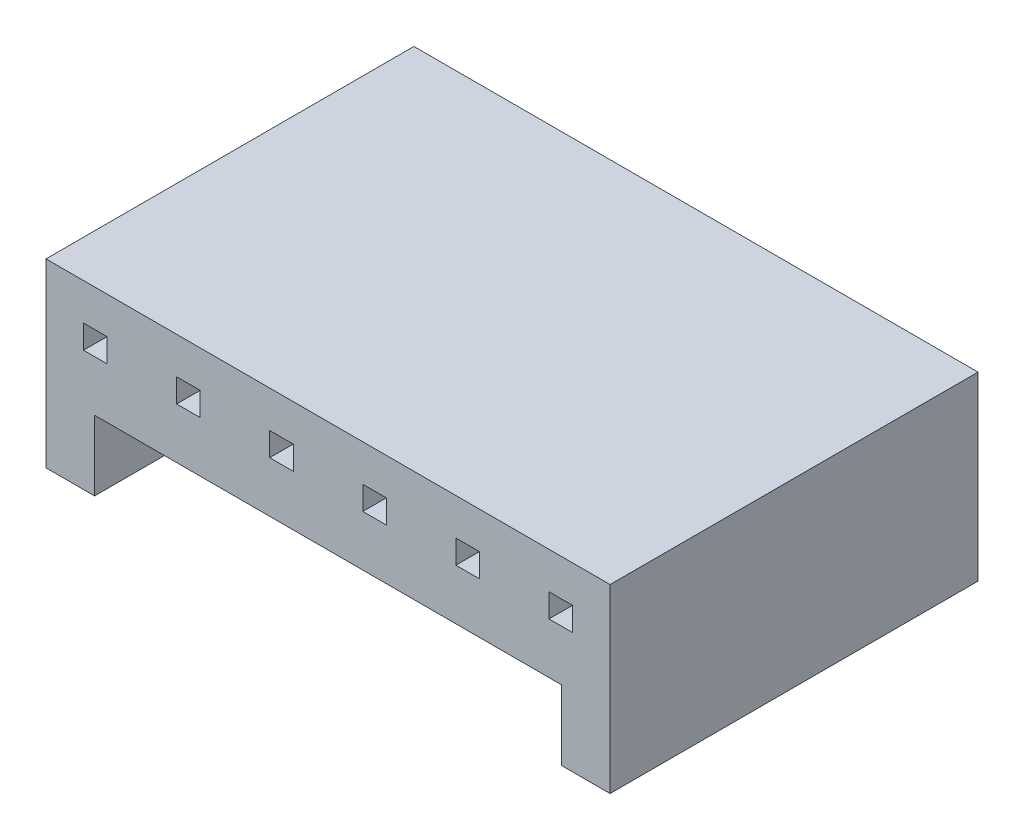
SolidWorks part; units mm, degrees
ref_plane "Front Plane" through (0, 0, 0) normal (0, 0, 1) x (1, 0, 0)
ref_plane "Top Plane" through (0, 0, 0) normal (0, 1, 0) x (1, 0, 0)
ref_plane "Right Plane" through (0, 0, 0) normal (1, 0, 0) x (0, 0, -1)
sketch "Sketch1" plane through (0, 0, 0) normal (0, 0, 1) x (1, 0, 0)
  line L0 (-39.4858, -35.6557) -> (-39.4858, -36.2957)
  line L1 (-42.0158, -35.6557) -> (-41.3758, -35.6557)
  line L2 (-42.0158, -35.6557) -> (-42.0158, -36.2957)
  line L3 (-42.0158, -36.2957) -> (-41.3758, -36.2957)
  line L4 (-41.3758, -35.6557) -> (-41.3758, -36.2957)
  line L5 (-42.0158, -35.6557) -> (-41.3758, -36.2957) construction
  line L6 (-42.0158, -36.2957) -> (-41.3758, -35.6557) construction
  line L7 (-39.4858, -35.6557) -> (-38.8458, -35.6557)
  line L8 (-38.8458, -35.6557) -> (-38.8458, -36.2957)
  line L9 (-39.4858, -36.2957) -> (-38.8458, -36.2957)
  line L10 (-36.9558, -35.6557) -> (-36.9558, -36.2957)
  line L11 (-36.9558, -35.6557) -> (-36.3158, -35.6557)
  line L12 (-36.3158, -35.6557) -> (-36.3158, -36.2957)
  line L13 (-36.9558, -36.2957) -> (-36.3158, -36.2957)
  line L14 (-34.4258, -35.6557) -> (-34.4258, -36.2957)
  line L15 (-34.4258, -35.6557) -> (-33.7858, -35.6557)
  line L16 (-33.7858, -35.6557) -> (-33.7858, -36.2957)
  line L17 (-34.4258, -36.2957) -> (-33.7858, -36.2957)
  line L18 (-31.8958, -35.6557) -> (-31.8958, -36.2957)
  line L19 (-31.8958, -35.6557) -> (-31.2558, -35.6557)
  line L20 (-31.2558, -35.6557) -> (-31.2558, -36.2957)
  line L21 (-31.8958, -36.2957) -> (-31.2558, -36.2957)
  line L22 (-29.3658, -35.6557) -> (-29.3658, -36.2957)
  line L23 (-29.3658, -35.6557) -> (-28.7258, -35.6557)
  line L24 (-28.7258, -35.6557) -> (-28.7258, -36.2957)
  line L25 (-29.3658, -36.2957) -> (-28.7258, -36.2957)
  line L26 (-42.0158, -35.6557) -> (-39.4858, -35.6557) construction
  line L27 (-43.0358, -34.6557) -> (-43.0358, -39.5757)
  line L28 (-43.0358, -34.6557) -> (-27.7058, -34.6557)
  line L29 (-43.0358, -35.6557) -> (-43.0358, -36.2957) construction
  line L30 (-42.0158, -34.6557) -> (-41.3758, -34.6557) construction
  line L31 (-43.0358, -39.5757) -> (-41.7158, -39.5757)
  line L32 (-41.7158, -39.5757) -> (-41.7158, -37.6757)
  line L33 (-36.3158, -35.6557) -> (-34.4258, -35.6557)
  line L34 (-35.3708, -35.6557) -> (-35.3708, -34.6557)
  line L35 (-41.7158, -37.6757) -> (-29.0258, -37.6757)
  line L36 (-29.0258, -39.5757) -> (-29.0258, -37.6757)
  line L37 (-27.7058, -39.5757) -> (-29.0258, -39.5757)
  line L38 (-27.7058, -34.6557) -> (-27.7058, -39.5757)
  line L39 (-39.4858, -35.6557) -> (-38.8458, -36.2957)
  line L40 (-39.4858, -36.2957) -> (-38.8458, -35.6557)
  line L41 (-36.9558, -35.6557) -> (-36.3158, -36.2957)
  line L42 (-36.3158, -35.6557) -> (-36.9558, -36.2957)
  point P0 (-41.6958, -35.9757)
  point P40 (-35.3708, -37.6757)
  point P42 (-39.1658, -35.9757)
  point P43 (-36.6358, -35.9757)
  point P44 (-34.1058, -35.9757)
  point P45 (-31.5758, -35.9757)
  point P46 (-29.0458, -35.9757)
  dimension "D1" = 6
  dimension "D2" = 2.53
  dimension "D3" = 1.02
  dimension "D4" = 1
extrude "Boss-Extrude1" add sketch "Sketch1" along normal blind 10
